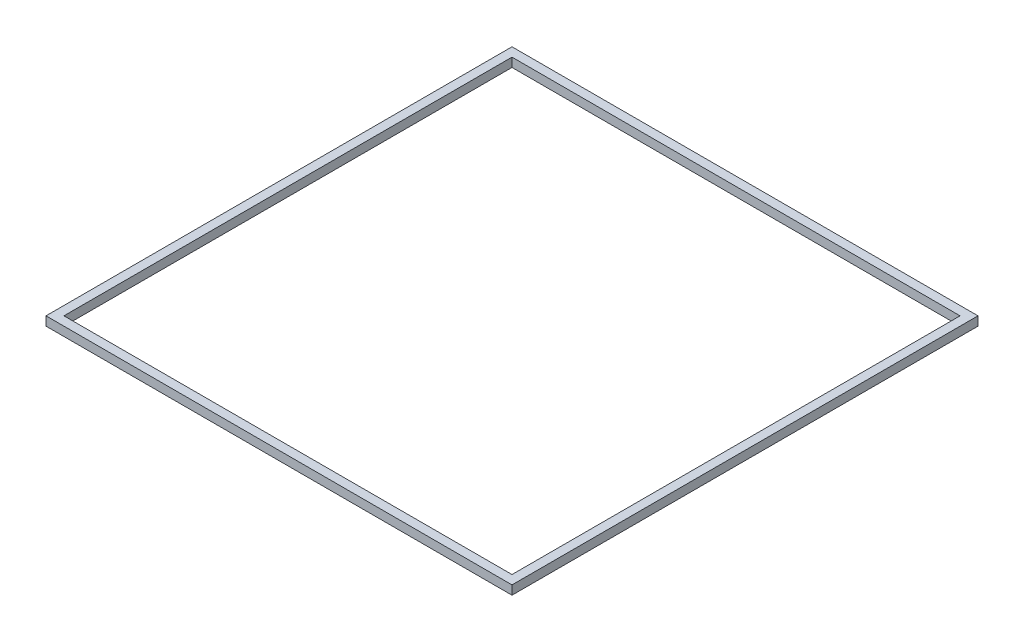
SolidWorks part; units mm, degrees
ref_plane "Front Plane" through (0, 0, 0) normal (0, 0, 1) x (1, 0, 0)
ref_plane "Top Plane" through (0, 0, 0) normal (0, 1, 0) x (1, 0, 0)
ref_plane "Right Plane" through (0, 0, 0) normal (1, 0, 0) x (0, 0, -1)
sketch "Sketch1" plane through (0, 0, 0) normal (0, 1, 0) x (1, 0, 0)
  line L0 (-52, 52) -> (52, 52)
  line L1 (-50, 50) -> (50, 50)
  line L2 (-50, 50) -> (-50, -50)
  line L3 (-50, -50) -> (50, -50)
  line L4 (50, 50) -> (50, -50)
  line L5 (-50, 50) -> (50, -50) construction
  line L6 (-50, -50) -> (50, 50) construction
  line L7 (52, 52) -> (52, -52)
  line L8 (-52, -52) -> (52, -52)
  line L9 (-52, 52) -> (-52, -52)
  point P0 (0, 0)
  dimension "D1" = 100
  dimension "D2" = 2
extrude "Boss-Extrude1" add sketch "Sketch1" along normal blind 2
